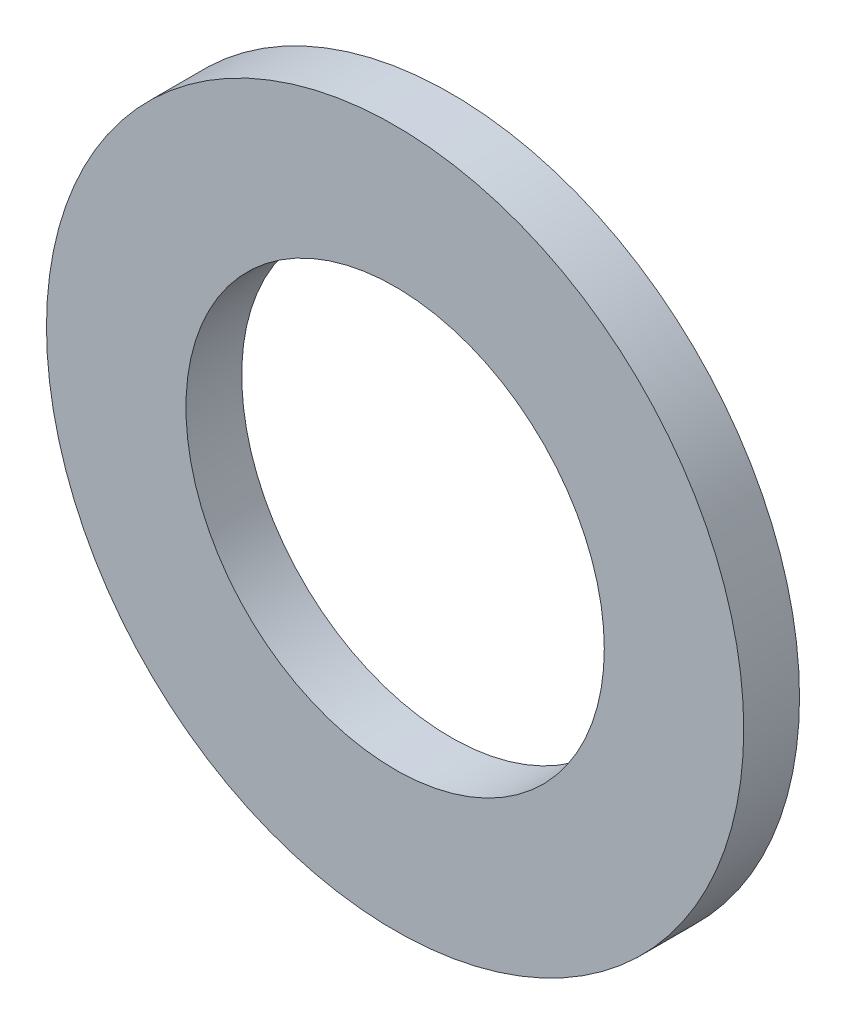
SolidWorks part; units mm, degrees
material "合金钢"
ref_plane "前视基准面" through (0, 0, 0) normal (0, 0, 1) x (1, 0, 0)
ref_plane "上视基准面" through (0, 0, 0) normal (0, 1, 0) x (1, 0, 0)
ref_plane "右视基准面" through (0, 0, 0) normal (1, 0, 0) x (0, 0, -1)
sketch "草图1" plane through (0, 0, 0) normal (0, 0, 1) x (1, 0, 0)
  circle A0 centre (0, 0) radius 1.5
  circle A1 centre (0, 0) radius 2.5
  dimension "D1" = 3
  dimension "D2" = 5
extrude "凸台-拉伸1" add sketch "草图1" along normal blind 0.4
equation "\"0。4\"=10"
